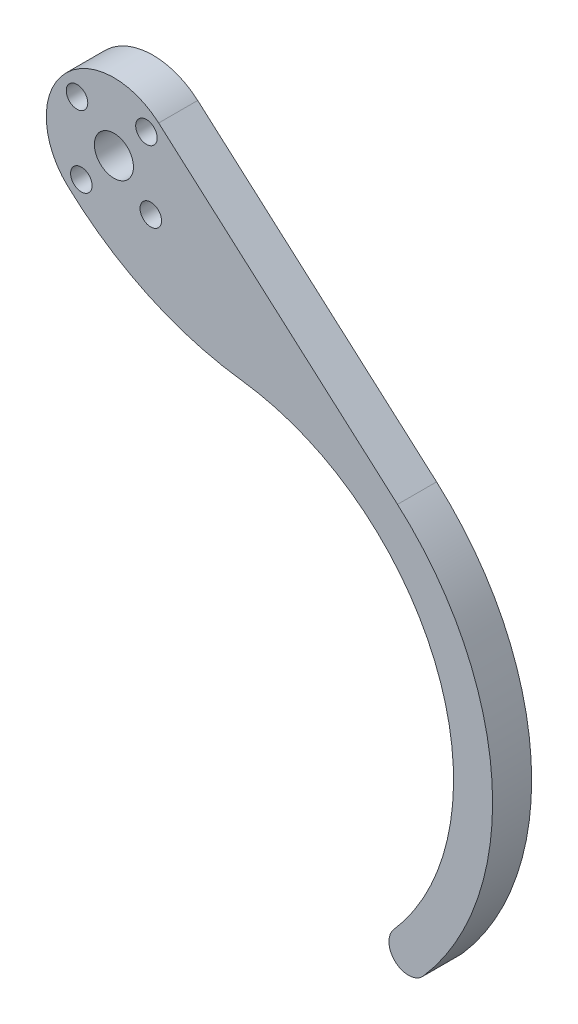
SolidWorks part; units mm, degrees
material "Plain Carbon Steel"
ref_plane "Front Plane" through (0, 0, 0) normal (0, 0, 1) x (1, 0, 0)
ref_plane "Top Plane" through (0, 0, 0) normal (0, 1, 0) x (1, 0, 0)
ref_plane "Right Plane" through (0, 0, 0) normal (1, 0, 0) x (0, 0, -1)
sketch "Sketch1" plane through (0, 0, 0) normal (0, 0, 1) x (1, 0, 0)
  line L2 (-15.875, 60.325) -> (0, 0) construction
  line L3 (-15.875, 60.325) -> (19.685, 60.325) construction
  line L4 (-8.5955, 68.5717) -> (30.2564, 34.2763)
  line L5 (0, 0) -> (10.5042, -39.916) construction
  arc A0 (29.6457, -25.9062) -> (4.9037, 39.0634) centre (0, 0) ccw
  arc A1 (-23.3666, 52.2704) -> (-8.5955, 68.5717) centre (-15.875, 60.325) cw
  arc A2 (-23.3666, 52.2704) -> (4.9037, 39.0634) centre (11.231, 89.4678) ccw
  arc A4 (29.6457, -25.9062) -> (34.4272, -30.0846) centre (32.0365, -27.9954) ccw
  arc A5 (34.4272, -30.0846) -> (30.2564, 34.2763) centre (0, 0) ccw
  circle A6 centre (-15.875, 60.325) radius 103.6539 construction
  point P0 (-15.875, 60.325)
  dimension "D3" = 11
  dimension "D4" = 39.37
  dimension "D5" = 6.35
  dimension "D7" = 50.8
  dimension "D8" = 41.275
  dimension "D6" = 35.56
extrude "Boss-Extrude1" add sketch "Sketch1" along normal blind 6.35
sketch "Sketch2" plane through (0, 0, 6.35) normal (0, 0, 1) x (1, 0, 0)
  line L0 (-15.875, 60.325) -> (-10.5808, 66.3226) construction
  line L1 (30.2564, 34.2763) -> (-8.5955, 68.5717) construction
  circle A0 centre (-15.875, 60.325) radius 3.175
  circle A1 centre (-10.5808, 66.3226) radius 1.75
  circle A2 centre (-9.8774, 55.0308) radius 1.75
  circle A3 centre (-21.1692, 54.3274) radius 1.75
  circle A4 centre (-21.8726, 65.6192) radius 1.75
  point P16 (-15.875, 60.325)
  dimension "D2" = 3.5
  dimension "D3" = 6.35
  dimension "D1" = 8
  dimension "D4" = 4
extrude "Cut-Extrude1" cut sketch "Sketch2" against normal through all
